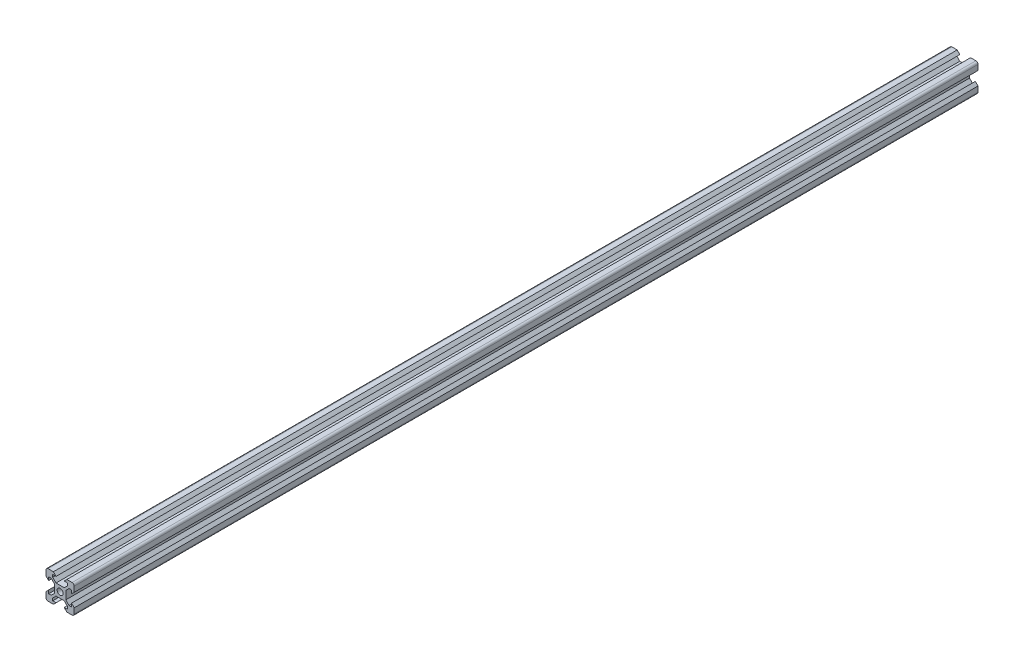
SolidWorks part; units mm, degrees
ref_plane "Front Plane" through (0, 0, 0) normal (0, 0, 1) x (1, 0, 0)
ref_plane "Top Plane" through (0, 0, 0) normal (0, 1, 0) x (1, 0, 0)
ref_plane "Right Plane" through (0, 0, 0) normal (1, 0, 0) x (0, 0, -1)
sketch "Sketch1" plane through (0, 0, 0) normal (0, 0, 1) x (1, 0, 0)
  line L0 (15.6876, 55.3211) -> (115.0437, 55.3211) construction
  line L1 (8.1, 5.225) -> (8.1, 2.85)
  line L2 (-8.5, 10) -> (-4.75, 10)
  line L3 (-10, 8.5) -> (-10, 4.75)
  line L4 (-8.5, -10) -> (-4.75, -10)
  line L5 (10, 8.5) -> (10, 4.75)
  line L6 (6.325, 5.225) -> (4, 2.9)
  line L7 (-8.1, -2.85) -> (-8.1, -5.225)
  line L8 (-2.9, 4) -> (2.9, 4)
  line L9 (-4, 2.9) -> (-4, -2.9)
  line L10 (-2.9, -4) -> (2.9, -4)
  line L11 (4, 2.9) -> (4, -2.9)
  line L12 (2.85, -8.1) -> (5.225, -8.1)
  line L13 (-5.225, -8.1) -> (-2.85, -8.1)
  line L14 (5.225, 6.325) -> (2.9, 4)
  line L17 (-10, 4.75) -> (-8.1, 2.85)
  line L20 (4.75, -10) -> (8.5, -10)
  line L22 (-10, -4.75) -> (-10, -8.5)
  line L23 (10, -4.75) -> (10, -8.5)
  line L24 (-10, -4.75) -> (-8.1, -2.85)
  line L25 (-4.75, -10) -> (-2.85, -8.1)
  line L26 (4.75, -10) -> (2.85, -8.1)
  line L27 (10, -4.75) -> (8.1, -2.85)
  line L28 (10, 4.75) -> (8.1, 2.85)
  line L29 (-4.75, 10) -> (-2.85, 8.1)
  line L30 (4.75, 10) -> (2.85, 8.1)
  line L31 (8.1, -2.85) -> (8.1, -5.225)
  line L32 (6.325, -5.225) -> (8.1, -5.225)
  line L33 (5.225, -6.325) -> (5.225, -8.1)
  line L34 (4.75, 10) -> (8.5, 10)
  line L35 (2.85, 8.1) -> (5.225, 8.1)
  line L36 (10, -10) -> (10.975, -10.975) construction
  line L37 (-5.225, 8.1) -> (-2.85, 8.1)
  line L38 (-8.1, -5.225) -> (-6.325, -5.225)
  line L39 (-5.225, 6.325) -> (-2.9, 4)
  line L40 (-8.1, 5.225) -> (-8.1, 2.85)
  line L41 (-5.225, -6.325) -> (-5.225, -8.1)
  line L42 (-6.325, 5.225) -> (-4, 2.9)
  line L46 (-8.1, 5.225) -> (-6.325, 5.225)
  line L47 (-5.225, 8.1) -> (-5.225, 6.325)
  line L52 (8.1, 5.225) -> (6.325, 5.225)
  line L53 (5.225, 8.1) -> (5.225, 6.325)
  line L63 (4, -2.9) -> (6.325, -5.225)
  line L66 (2.9, -4) -> (5.225, -6.325)
  line L67 (-2.9, -4) -> (-5.225, -6.325)
  line L70 (-4, -2.9) -> (-6.325, -5.225)
  arc A0 (-8.5, -10) -> (-10, -8.5) centre (-8.5, -8.5) cw
  arc A1 (8.5, -10) -> (10, -8.5) centre (8.5, -8.5) ccw
  arc A2 (10, 8.5) -> (8.5, 10) centre (8.5, 8.5) ccw
  arc A3 (-8.5, 10) -> (-10, 8.5) centre (-8.5, 8.5) ccw
  circle A4 centre (0, 0) radius 2.125
  point P2 (0, 0)
  point P8 (0, 0)
  point P14 (-10, -10)
  point P20 (0, 0)
  point P49 (10, 10)
  point P52 (-10, 10)
  dimension "D3" = 1.5
  dimension "D4" = 4.25
  dimension "D1" = 20
  dimension "D2" = 20
  dimension "D13" = 5.25
  dimension "D14" = 5.25
  dimension "D15" = 90
  dimension "D16" = 5.25
  dimension "D17" = 5.25
  dimension "D18" = 5.25
  dimension "D19" = 5.25
  dimension "D20" = 5.25
  dimension "D21" = 5.25
  dimension "D22" = 90
  dimension "D23" = 90
  dimension "D24" = 90
  dimension "D25" = 2.85
  dimension "D26" = 2.85
  dimension "D27" = 2.85
  dimension "D28" = 2.85
extrude "Boss-Extrude1" add sketch "Sketch1" along normal blind 640
